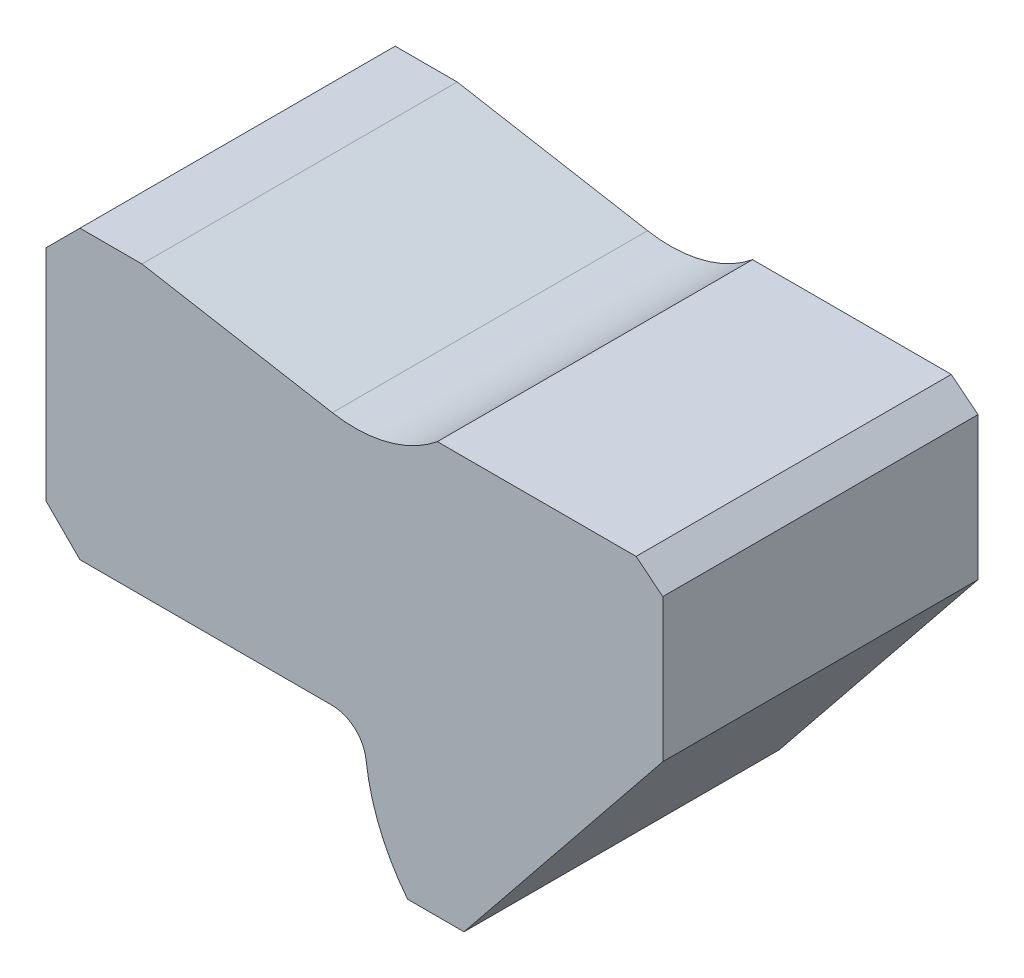
SolidWorks part; units mm, degrees
ref_plane "Płaszczyzna przednia" through (0, 0, 0) normal (0, 0, 1) x (1, 0, 0)
ref_plane "Płaszczyzna górna" through (0, 0, 0) normal (0, 1, 0) x (1, 0, 0)
ref_plane "Płaszczyzna prawa" through (0, 0, 0) normal (1, 0, 0) x (0, 0, -1)
other "Tabela konfiguracji"
sketch "Szkic1" plane through (0, 0, 0) normal (0, 0, 1) x (1, 0, 0)
  line L0 (0, 0) -> (8.2376, 0)
  line L1 (8.2376, 0) -> (37.2376, 36)
  line L2 (37.2376, 36) -> (37.2376, 56.8634)
  line L3 (37.2376, 56.8634) -> (33.3439, 60)
  line L4 (33.3439, 60) -> (4.3439, 60)
  line L6 (-38.7624, 60.8995) -> (-47.8126, 60.8995)
  line L10 (-47.8126, 19) -> (-11.0263, 19)
  line L11 (-47.8126, 60.8995) -> (-52.7624, 55.9497)
  line L12 (-47.8126, 19) -> (-52.7624, 23.9497)
  line L13 (-52.7624, 55.9497) -> (-52.7624, 23.9497)
  line L14 (-38.7624, 60.8995) -> (-10.9788, 56.0005)
  arc A1 (-11.0263, 19) -> (-6.061, 14.5882) centre (-11.0263, 14) cw
  arc A3 (-6.061, 14.5882) -> (0, 0) centre (22.7376, 18) ccw
  arc A4 (4.3439, 60) -> (-10.9788, 56.0005) centre (-7.6795, 74.7119) cw
  point P20 (-7.7052, 17.7377)
  dimension "D8" = 29
  dimension "D2" = 19
  dimension "D3" = 29
  dimension "D4" = 29
  dimension "D5" = 24
  dimension "B" = 60
  dimension "D7" = 5
  dimension "D10" = 32
  dimension "A" = 90
  dimension "D11" = 14
  dimension "D12" = 45
  dimension "D13" = 45
  dimension "D14" = 19
  dimension "D15" = 7
  dimension "D16" = 5
  dimension "D17" = 10
extrude "Dodanie-wyciągnięcie1" add sketch "Szkic1" along normal blind 46
